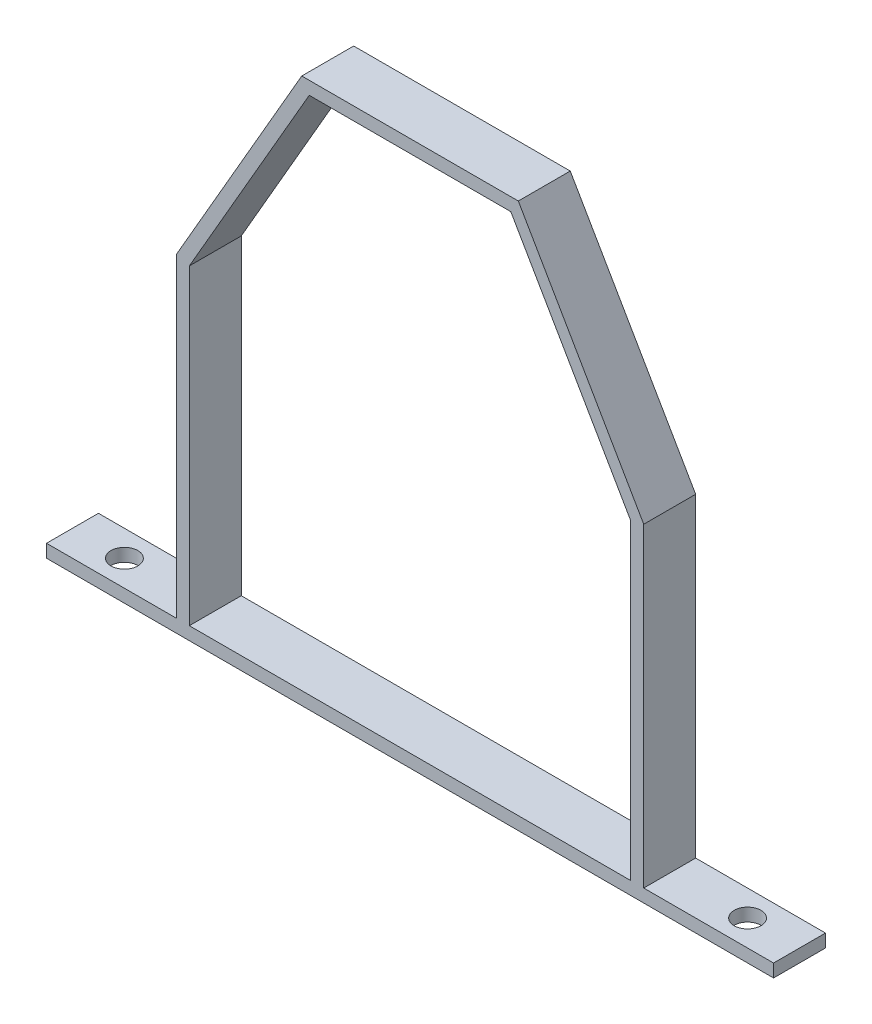
SolidWorks part; units mm, degrees
ref_plane "Front Plane" through (0, 0, 0) normal (0, 0, 1) x (1, 0, 0)
ref_plane "Top Plane" through (0, 0, 0) normal (0, 1, 0) x (1, 0, 0)
ref_plane "Right Plane" through (0, 0, 0) normal (1, 0, 0) x (0, 0, -1)
sketch "Sketch1" plane through (0, 0, 0) normal (0, 0, 1) x (1, 0, 0)
  line L0 (0, 0) -> (-355.6, 0)
  line L1 (-355.6, 0) -> (-355.6, 6.35)
  line L2 (-63.5, 6.35) -> (0, 6.35)
  line L3 (0, 6.35) -> (0, 0)
  line L4 (-355.6, 6.35) -> (-292.1, 6.35)
  line L5 (-292.1, 6.35) -> (-292.1, 160.4515)
  line L7 (-285.75, 158.75) -> (-285.75, 6.35)
  line L8 (-285.75, 6.35) -> (-69.85, 6.35)
  line L9 (-69.85, 6.35) -> (-69.85, 158.75)
  line L11 (-63.5, 160.4515) -> (-63.5, 6.35)
  line L12 (-177.8, 6.35) -> (-177.8, 0) construction
  line L13 (-292.1, 160.4515) -> (-230.7574, 266.7)
  line L14 (-230.7574, 266.7) -> (-124.8426, 266.7)
  line L15 (-124.8426, 266.7) -> (-63.5, 160.4515)
  line L16 (-69.85, 158.75) -> (-128.5088, 260.35)
  line L17 (-128.5088, 260.35) -> (-227.0912, 260.35)
  line L18 (-227.0912, 260.35) -> (-285.75, 158.75)
  line L19 (-285.75, 158.75) -> (-69.85, 158.75) construction
  dimension "D1" = 6.35
  dimension "D2" = 355.6
  dimension "D3" = 6.35
  dimension "D4" = 6.35
  dimension "D5" = 215.9
  dimension "D6" = 150
  dimension "D7" = 152.4
  dimension "D8" = 150
  dimension "D9" = 6.35
  dimension "D10" = 6.35
  dimension "D11" = 6.35
  dimension "D12" = 101.6
extrude "Boss-Extrude1" add sketch "Sketch1" along normal blind 25.4
hole_wizard "1/2 Clearance Hole1" positions "Sketch2" profile "Sketch3" hole size "1/2" standard "ANSI Inch"
sketch "Sketch2" plane through (0, 0, 0) normal (0, -1, 0) x (-1, 0, 0)
  line L0 (25.4, -12.7) -> (330.2, -12.7) construction
  line L2 (177.8, -12.7) -> (177.8, 0) construction
  line L3 (355.6, 0) -> (0, 0) construction
  point P0 (25.4, -12.7)
  point P2 (330.2, -12.7)
  dimension "D1" = 304.8
  dimension "D2" = 12.7
sketch "Sketch3" plane through (-25.4, 0, 12.7) normal (1, 0, 0) x (0, 0, -1)
  line L0 (0, 0) -> (0, 80.1345)
  line L1 (0, 80.1345) -> (6.5481, 76.2)
  line L2 (6.5481, 76.2) -> (6.5481, 0)
  line L5 (6.5481, 0) -> (0, 0)
  line L10 (0, 80.1345) -> (-6.5481, 76.2) construction
  line L11 (0, -6.35) -> (0, 107.95) construction
  dimension "Hole Dia." = 13.0962
  dimension "Hole Depth" = 76.2
  dimension "Drill Angle" = 118
